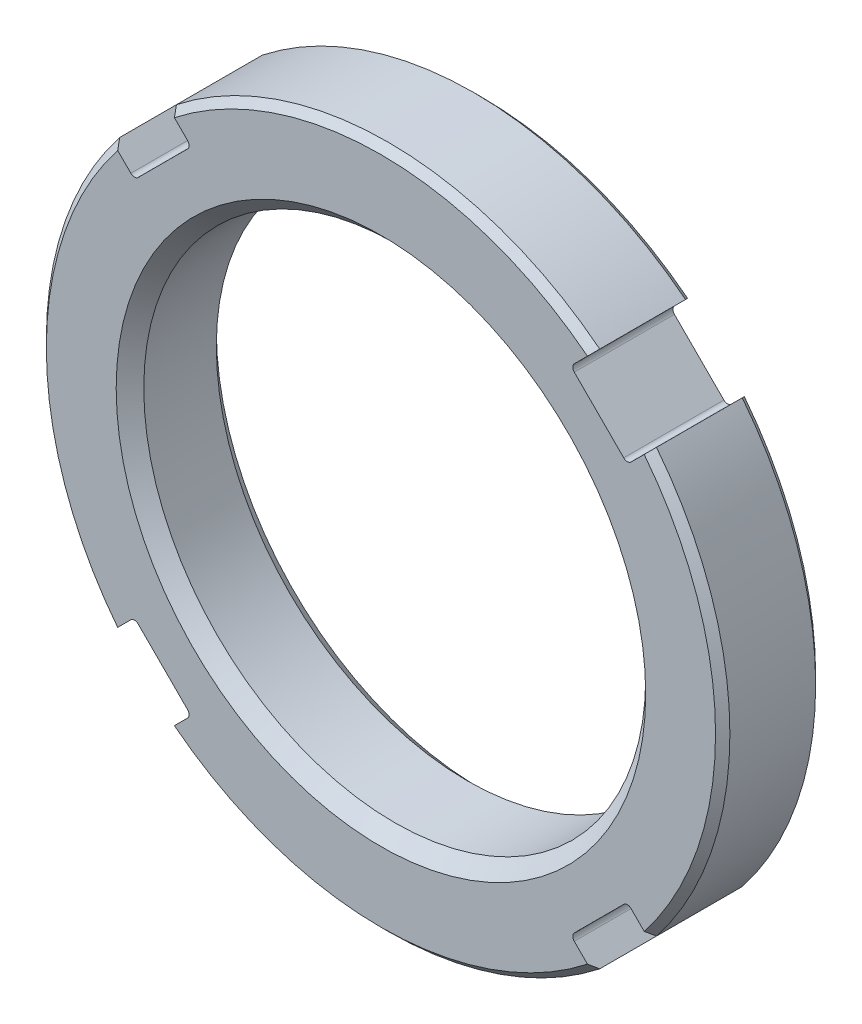
SolidWorks part; units mm, degrees
material "Alloy Steel"
ref_plane "Front Plane" through (0, 0, 0) normal (0, 0, 1) x (1, 0, 0)
ref_plane "Top Plane" through (0, 0, 0) normal (0, 1, 0) x (1, 0, 0)
ref_plane "Right Plane" through (0, 0, 0) normal (1, 0, 0) x (0, 0, -1)
sketch "Sketch1" plane through (0, 0, 0) normal (0, 0, 1) x (1, 0, 0)
  circle A0 centre (0, 0) radius 27.051
  circle A1 centre (0, 0) radius 19.8628
  dimension "D1" = 54.102
  dimension "D2" = 39.7256
extrude "Extrude1" add sketch "Sketch1" along normal blind 7.9248
chamfer "Chamfer1" distance 0.5679 angle 45 2 edges at (27.051, 0, 0) (27.051, 0, 7.9248)
chamfer "Chamfer2" distance 1.0922 angle 45 2 edges at (19.8628, 0, 0) (19.8628, 0, 7.9248)
sketch "Sketch2" plane through (0, 0, 7.9248) normal (0, 0, 1) x (1, 0, 0)
  line L0 (0, 0) -> (22.7176, 0) construction
  line L1 (0, 0) -> (15.6425, 15.6425) construction
  line L2 (16.7507, 21.2408) -> (15.015, 19.5051)
  line L3 (15.015, 19.5051) -> (19.5051, 15.015)
  line L4 (21.2408, 16.7507) -> (19.5051, 15.015)
  circle A0 centre (0, 0) radius 27.051 construction
  arc A1 (21.2408, 16.7507) -> (16.7507, 21.2408) centre (0, 0) ccw
  dimension "D3" = 2.6416
  dimension "D1" = 45
  dimension "D2" = 6.35
extrude "Cut-Extrude1" cut sketch "Sketch2" against normal through all
fillet "Fillet1" radius 0.4064 2 edges at (19.5051, 15.015, 3.9624) (15.015, 19.5051, 3.9624)
pattern_circular "CirPattern1" count 4 over 360 about axis through (0, 0, 0) along (0, 0, 1) of "Fillet1", "Cut-Extrude1"
